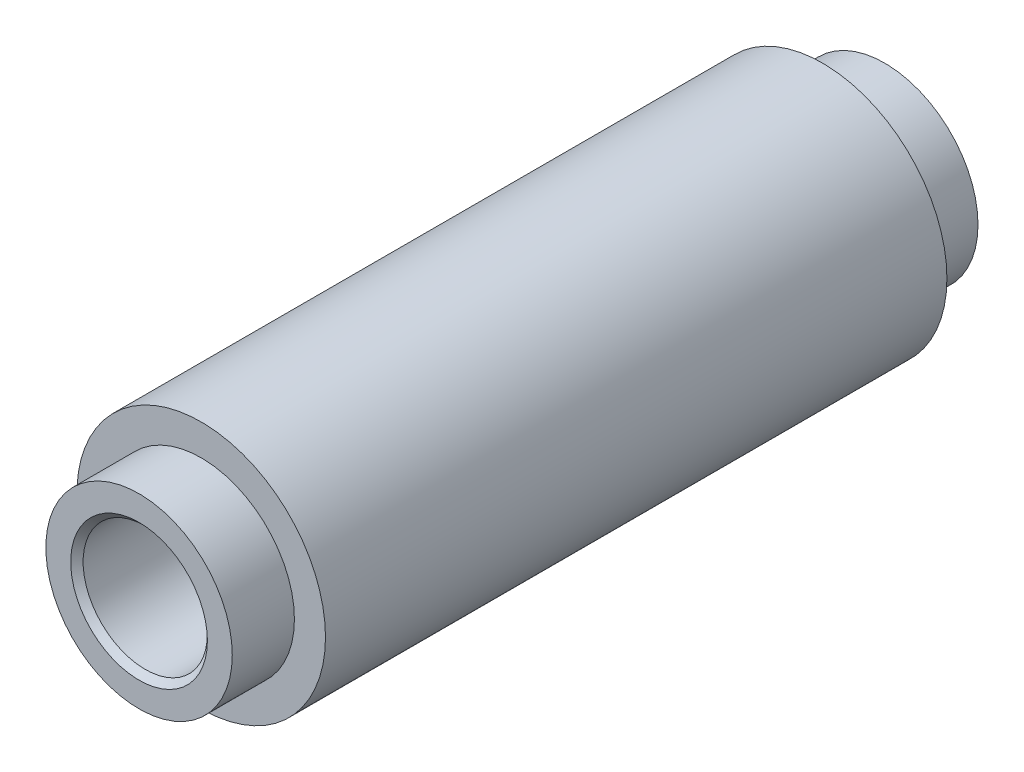
SolidWorks part; units mm, degrees
material "Plain Carbon Steel"
ref_plane "Front Plane" through (0, 0, 0) normal (0, 0, 1) x (1, 0, 0)
ref_plane "Top Plane" through (0, 0, 0) normal (0, 1, 0) x (1, 0, 0)
ref_plane "Right Plane" through (0, 0, 0) normal (1, 0, 0) x (0, 0, -1)
sketch "Sketch1" plane through (0, 0, 0) normal (0, 0, 1) x (1, 0, 0)
  circle A0 centre (0, 0) radius 4
  dimension "D1" = 8
extrude "Boss-Extrude1" add sketch "Sketch1" along normal blind 10
sketch "Sketch2" plane through (0, 0, 10) normal (0, 0, 1) x (1, 0, 0)
  circle A0 centre (0, 0) radius 3
  dimension "D1" = 6
extrude "Boss-Extrude2" add sketch "Sketch2" along normal blind 2
mirror "Mirror1" about plane through (0, 0, 0) normal (0, 0, 1) of "Boss-Extrude2", "Boss-Extrude1"
sketch "Sketch3" plane through (0, 0, 12) normal (0, 0, 1) x (1, 0, 0)
  circle A0 centre (0, 0) radius 2
  dimension "D1" = 4
extrude "Cut-Extrude1" cut sketch "Sketch3" against normal through all
cosmetic thread "Cosmetic Thread1" parameters "D1"=23.6, "D2"=5
chamfer "Chamfer1" distance 0.2 angle 45 2 edges at (2, 0, 12) (2, 0, -12)
